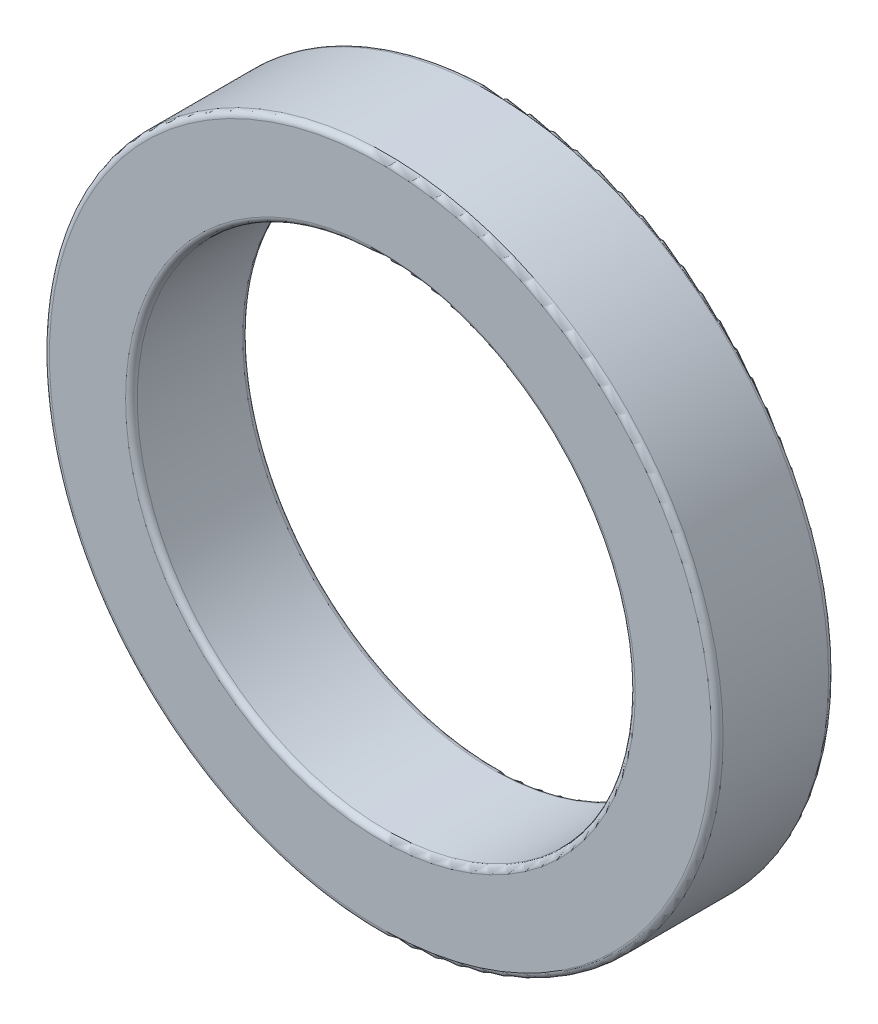
SolidWorks part; units mm, degrees
ref_plane "前视基准面" through (0, 0, 0) normal (0, 0, 1) x (1, 0, 0)
ref_plane "上视基准面" through (0, 0, 0) normal (0, 1, 0) x (1, 0, 0)
ref_plane "右视基准面" through (0, 0, 0) normal (1, 0, 0) x (0, 0, -1)
sketch "草图1" plane through (0, 0, 0) normal (0, 0, 1) x (1, 0, 0)
  circle A0 centre (0, 0) radius 8.5
  circle A1 centre (0, 0) radius 11.5
  dimension "D1" = 17
  dimension "D2" = 23
extrude "凸台-拉伸1" add sketch "草图1" along normal blind 4
fillet "圆角1" radius 0.2 4 edges at (8.5, 0, 0) (11.5, 0, 0) (8.5, 0, 4) (11.5, 0, 4)
